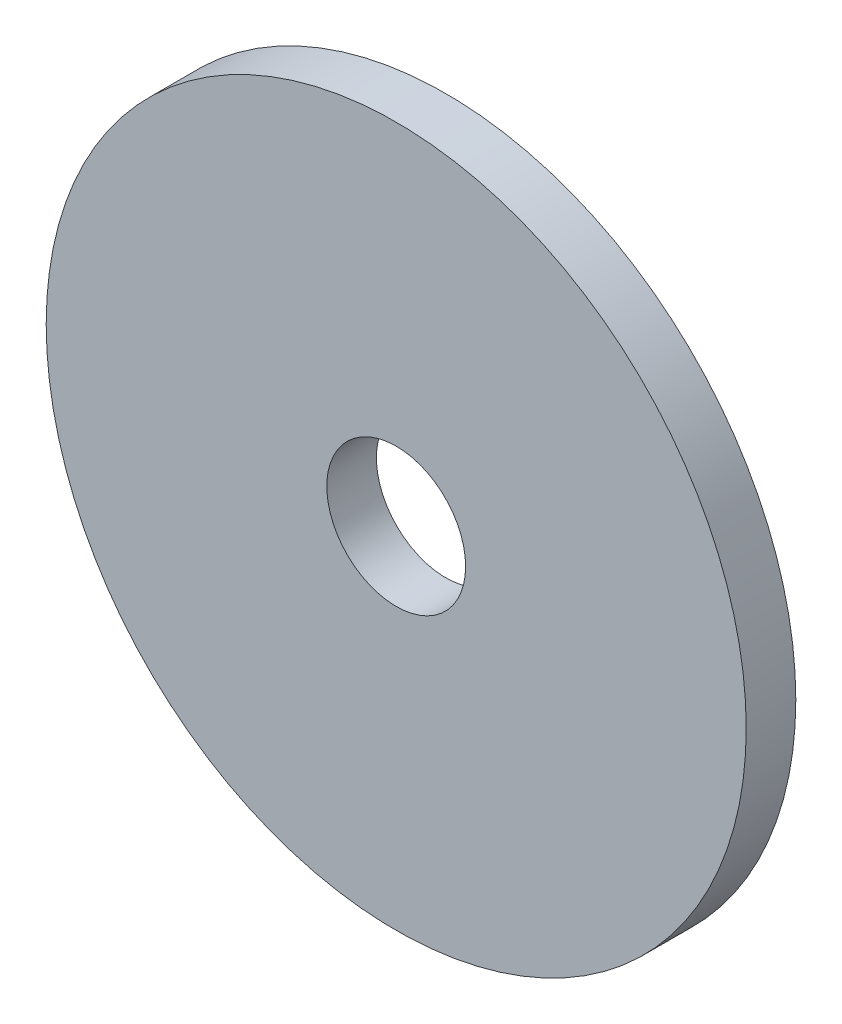
SolidWorks part; units mm, degrees
material "PE Low/Medium Density"
ref_plane "Front Plane" through (0, 0, 0) normal (0, 0, 1) x (1, 0, 0)
ref_plane "Top Plane" through (0, 0, 0) normal (0, 1, 0) x (1, 0, 0)
ref_plane "Right Plane" through (0, 0, 0) normal (1, 0, 0) x (0, 0, -1)
sketch "Sketch1" plane through (0, 0, 0) normal (0, 0, 1) x (1, 0, 0)
  circle A0 centre (0, 0) radius 4.4831
  circle A1 centre (0, 0) radius 0.889
  dimension "D1" = 8.9662
  dimension "D2" = 1.778
extrude "Plate" add sketch "Sketch1" along normal blind 0.635
